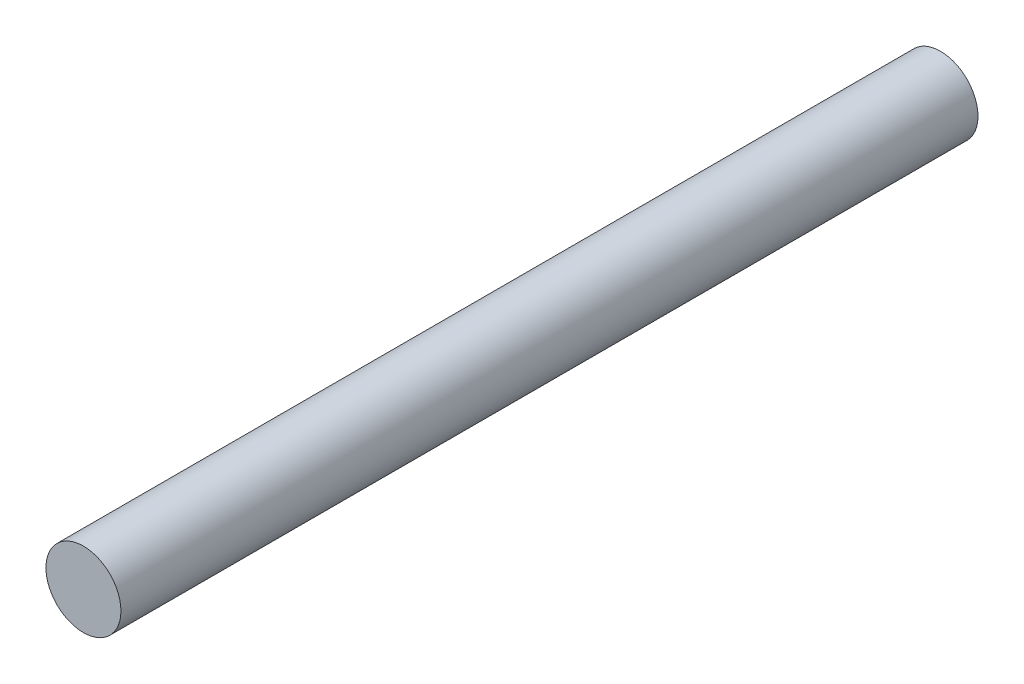
SolidWorks part; units mm, degrees
ref_plane "Alzado" through (0, 0, 0) normal (0, 0, 1) x (1, 0, 0)
ref_plane "Planta" through (0, 0, 0) normal (0, 1, 0) x (1, 0, 0)
ref_plane "Vista lateral" through (0, 0, 0) normal (1, 0, 0) x (0, 0, -1)
sketch "Croquis1" plane through (0, 0, 0) normal (0, 0, 1) x (1, 0, 0)
  circle A0 centre (0, 0) radius 1.75
extrude "Saliente-Extruir1" add sketch "Croquis1" along normal blind 40
